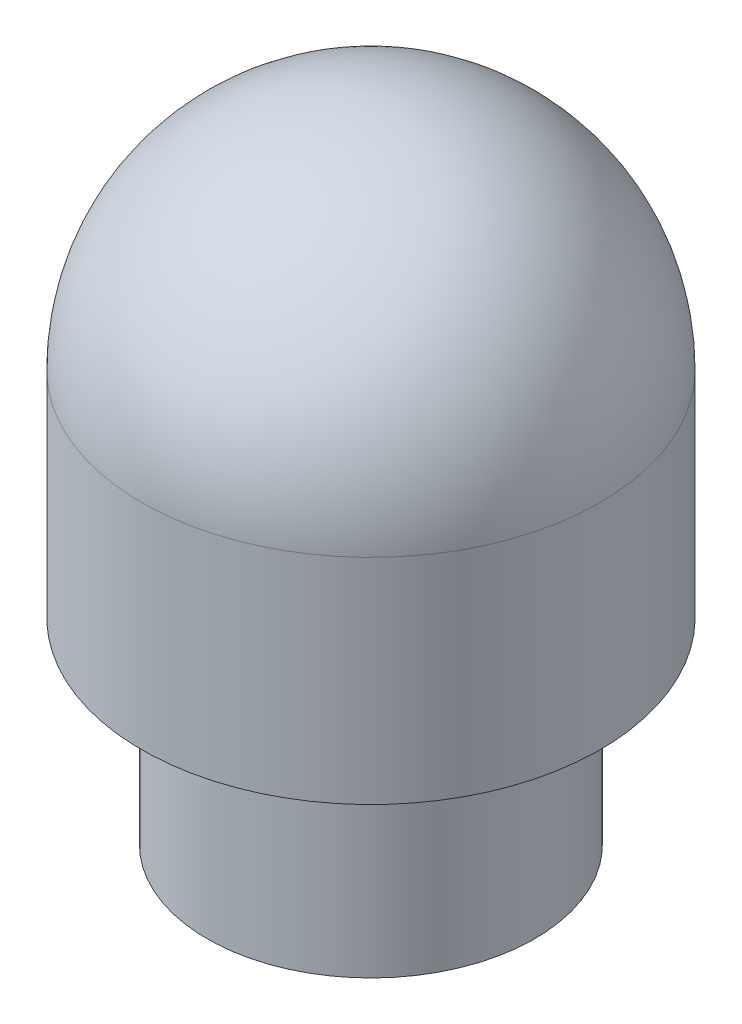
SolidWorks part; units mm, degrees
material "ABS PC"
ref_plane "Front Plane" through (0, 0, 0) normal (0, 0, 1) x (1, 0, 0)
ref_plane "Top Plane" through (0, 0, 0) normal (0, 1, 0) x (1, 0, 0)
ref_plane "Right Plane" through (0, 0, 0) normal (1, 0, 0) x (0, 0, -1)
sketch "Sketch2" plane through (0, 0, 0) normal (1, 0, 0) x (0, 0, -1)
  line L0 (0, 0) -> (0, 15.5067) construction
  line L1 (0, 0) -> (0, 15.5067)
  line L3 (5.5563, 4.7625) -> (3.9688, 4.7625)
  line L4 (3.9688, 4.7625) -> (3.9688, 0)
  line L5 (3.9688, 0) -> (0, 0)
  line L6 (5.5563, 9.9505) -> (5.5563, 4.7625)
  arc A0 (0, 15.5067) -> (5.5563, 9.9505) centre (0, 9.9505) cw
  dimension "D1" = 11.1125
  dimension "D2" = 7.9375
  dimension "D3" = 10.7442
  dimension "D4" = 4.7625
revolve "Revolve1" add sketch "Sketch2" angle 360 about L0
sketch "Sketch3" plane through (0, 0, 0) normal (0, -1, 0) x (1, 0, 0)
  circle A0 centre (0, 0) radius 3
  dimension "D1" = 6
extrude "Cut-Extrude1" cut sketch "Sketch3" against normal blind 13.97
fillet "Fillet1" radius 3 1 edges at (0, 13.97, -3)
